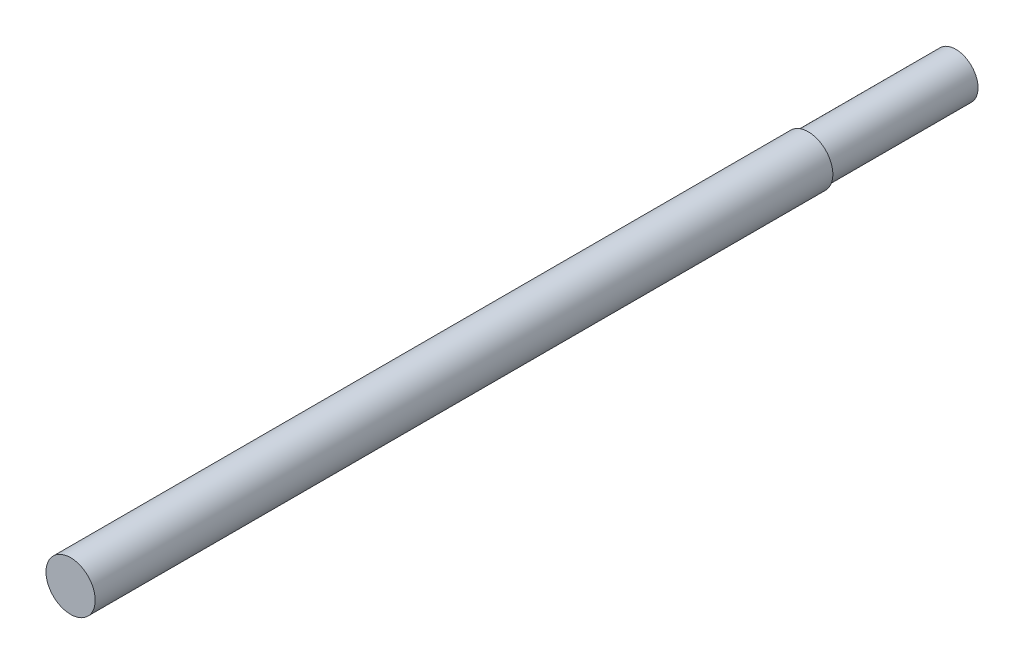
SolidWorks part; units mm, degrees
ref_plane "Front Plane" through (0, 0, 0) normal (0, 0, 1) x (1, 0, 0)
ref_plane "Top Plane" through (0, 0, 0) normal (0, 1, 0) x (1, 0, 0)
ref_plane "Right Plane" through (0, 0, 0) normal (1, 0, 0) x (0, 0, -1)
sketch "Sketch1" plane through (0, 0, 0) normal (0, 0, 1) x (1, 0, 0)
  line L1 (-25.4, 0) -> (25.4, 0) construction
  dimension "OD" = 50.8
sketch "Sketch2" plane through (0, 0, 0) normal (1, 0, 0) x (0, 0, -1)
  line L0 (457.2, 0) -> (-457.2, 0)
  point P4 (0, 0)
  dimension "Length" = 914.4
sketch "Sketch3" plane through (0, 0, 0) normal (0, 0, 1) x (1, 0, 0)
  circle A0 centre (0, 0) radius 25.4
extrude "Boss-Extrude1" add sketch "Sketch3" along normal up to vertex (457.2 mm away) and the other way up to vertex (457.2 mm away) up to point (0, 0, 457.2) other way up to point (0, 0, -457.2)
sketch "Sketch4" plane through (0, 0, -457.2) normal (0, 0, 1) x (1, 0, 0)
  circle A0 centre (0, 0) radius 9.525
  dimension "D1" = 19.05
extrude "Cut-Extrude2" cut sketch "Sketch4" along normal blind 19.05
sketch "Sketch5" plane through (0, 0, -457.2) normal (0, 0, -1) x (-1, 0, 0)
  circle A0 centre (0, 0) radius 23
  circle A2 centre (0, 0) radius 25.4
  dimension "D1" = 46
extrude "Cut-Extrude3" cut sketch "Sketch5" against normal blind 152.4
